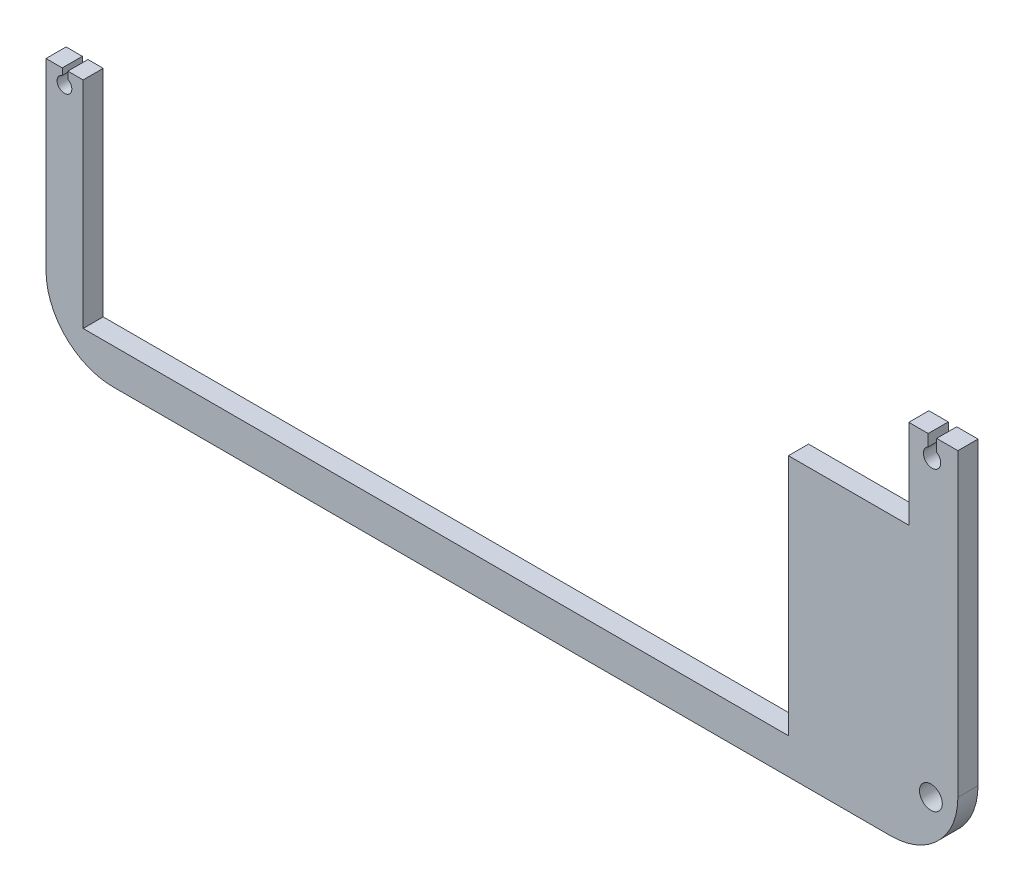
SolidWorks part; units mm, degrees
ref_plane "Front Plane" through (0, 0, 0) normal (0, 0, 1) x (1, 0, 0)
ref_plane "Top Plane" through (0, 0, 0) normal (0, 1, 0) x (1, 0, 0)
ref_plane "Right Plane" through (0, 0, 0) normal (1, 0, 0) x (0, 0, -1)
sketch "Sketch1" plane through (0, 0, 0) normal (0, 0, 1) x (1, 0, 0)
  line L8 (-93.5366, 73.7988) -> (22.5267, 73.7988)
  line L9 (32.5267, 83.7988) -> (32.5267, 133.7988)
  line L10 (22.5267, 143.7988) -> (-93.5366, 143.7988)
  line L11 (-103.5366, 133.7988) -> (-103.5366, 83.7988)
  line L24 (7.2413, 79.1138) -> (7.2413, 115.2988)
  line L25 (7.2413, 115.2988) -> (25.2005, 115.2988)
  line L26 (25.2005, 115.2988) -> (25.2005, 141.2988)
  line L27 (25.2005, 141.2988) -> (-63.6861, 141.2988)
  line L28 (-63.6861, 141.2988) -> (-63.6861, 139.2988)
  line L29 (-63.6861, 139.2988) -> (-98, 139.2988)
  line L30 (-98, 139.2988) -> (-98, 79.1138)
  line L31 (-98, 79.1138) -> (7.2413, 79.1138)
  arc A8 (22.5267, 73.7988) -> (32.5267, 83.7988) centre (22.5267, 83.7988) ccw
  arc A9 (32.5267, 133.7988) -> (22.5267, 143.7988) centre (22.5267, 133.7988) ccw
  arc A10 (-93.5366, 143.7988) -> (-103.5366, 133.7988) centre (-93.5366, 133.7988) ccw
  arc A11 (-103.5366, 83.7988) -> (-93.5366, 73.7988) centre (-93.5366, 83.7988) ccw
extrude "Boss-Extrude1" add sketch "Sketch1" along normal blind 3
sketch "Sketch2" plane through (0, 0, 3) normal (0, 0, 1) x (1, 0, 0)
  line L0 (-98, 111.233) -> (-100.276, 111.233)
  line L1 (-101.1106, 111.233) -> (-103.5366, 111.233)
  line L2 (-101.1106, 110.2573) -> (-101.1106, 111.233)
  line L3 (28.0964, 126.8564) -> (28.0964, 128.5916)
  line L4 (-100.276, 110.1813) -> (-100.276, 111.233)
  line L5 (-98, 139.2988) -> (-98, 79.1138) construction
  line L6 (-103.5366, 133.7988) -> (-103.5366, 83.7988) construction
  line L7 (28.0964, 128.5916) -> (25.2005, 128.5916)
  line L8 (25.2005, 115.2988) -> (25.2005, 141.2988) construction
  line L9 (32.5267, 128.5916) -> (29.357, 128.5916)
  line L10 (32.5267, 83.7988) -> (32.5267, 133.7988) construction
  line L11 (29.357, 128.5916) -> (29.357, 126.7956)
  line L12 (-103.5366, 111.233) -> (-103.5366, 155.1691)
  line L13 (-103.5366, 155.1691) -> (37.5209, 146.4954)
  line L14 (37.5209, 146.4954) -> (36.42, 128.5916)
  line L15 (36.42, 128.5916) -> (32.5267, 128.5916)
  line L16 (25.2005, 128.5916) -> (-98, 111.233)
  arc A0 (-101.1106, 110.2573) -> (-100.276, 110.1813) centre (-100.7855, 109.2063) ccw
  arc A1 (28.0964, 126.8564) -> (29.357, 126.7956) centre (28.6722, 125.6963) ccw
hole_wizard "M3 Clearance Hole1" positions "Sketch4" profile "Sketch3" hole size "M3" standard "ISO" end condition through all
sketch "Sketch4" plane through (0, 0, 0) normal (0, 0, -1) x (-1, 0, 0)
  point P0 (-28.4975, 136.7988)
  point P2 (-28.4975, 81.7988)
sketch "Sketch3" plane through (28.4975, 136.7988, 0) normal (1, 0, 0) x (0, 1, 0)
  line L0 (0, 0) -> (0, 3)
  line L1 (0, 3) -> (1.7, 3)
  line L2 (1.7, 3) -> (1.7, 0)
  line L5 (1.7, 0) -> (0, 0)
  line L11 (0, -6.35) -> (0, 107.95) construction
  dimension "Thru Hole Dia." = 3.4
  dimension "Thru Hole Depth" = 3
extrude "Cut-Extrude1" cut sketch "Sketch2" against normal blind 10
